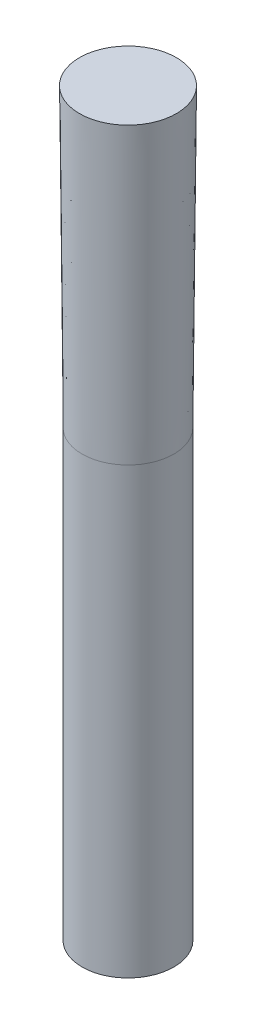
SolidWorks part; units mm, degrees
ref_plane "Přední rovina" through (0, 0, 0) normal (0, 0, 1) x (1, 0, 0)
ref_plane "Vrchní rovina" through (0, 0, 0) normal (0, 1, 0) x (1, 0, 0)
ref_plane "Pravá rovina" through (0, 0, 0) normal (1, 0, 0) x (0, 0, -1)
sketch "Skica1" plane through (0, 0, 0) normal (0, 1, 0) x (1, 0, 0)
  circle A0 centre (0, 0) radius 3.1
  dimension "D1" = 6.2
extrude "Přidat vysunutím1" add sketch "Skica1" along normal blind 30
sketch "Skica2" plane through (0, 30, 0) normal (0, 1, 0) x (1, 0, 0)
  circle A1 centre (0, 0) radius 3.1
  circle A2 centre (0, 0) radius 3.1
  dimension "D1" = 0
extrude "Přidat vysunutím2" add sketch "Skica2" along normal blind 20 draft 0.5 draft outward yes
